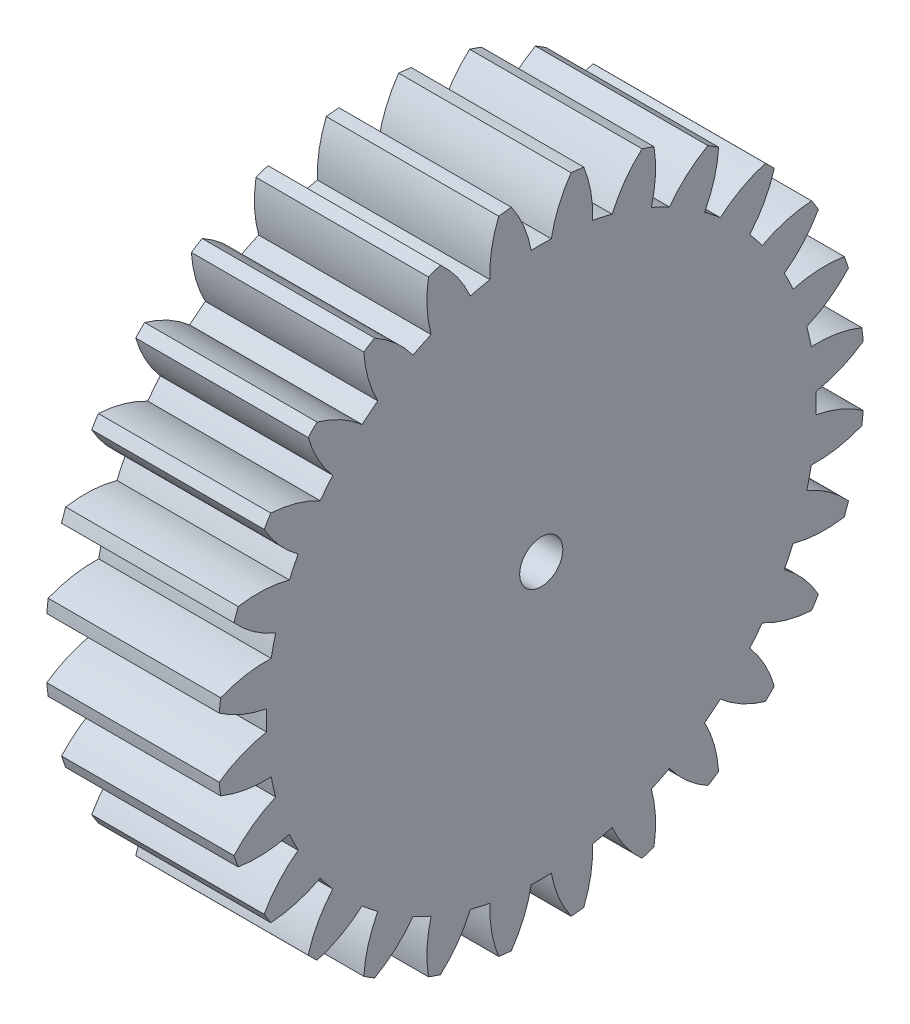
SolidWorks part; units mm, degrees
ref_plane "Plane1" through (0, 0, 0) normal (0, 0, 1) x (1, 0, 0)
ref_plane "Plane2" through (0, 0, 0) normal (0, 1, 0) x (1, 0, 0)
ref_plane "Plane3" through (0, 0, 0) normal (1, 0, 0) x (0, 0, -1)
sketch "HoldingSke" plane through (0, 0, 0) normal (0, 1, 0) x (1, 0, 0)
  line L0 (0, 0) -> (0.3532, -0.1878)
  line L1 (-15, 0) -> (100, 0) construction
  line L2 (0, 0) -> (-2.1039, 2.3779)
  line L3 (0, 0) -> (-11.863, 4.5341)
  line L4 (0, 0) -> (7.6251, 4.0544)
  line L5 (0, 0) -> (-46.8476, -17.4728)
  line L6 (0, 0) -> (-16.5793, -11.1861)
  line L7 (-2.1039, 2.3779) -> (8.6586, 51.2059)
  line L8 (-76.2, 54.61) -> (-75.3, 54.61)
  line L9 (-71.009, 38.7566) -> (-53.1078, 45.2721)
  line L10 (-76.2, 71.12) -> (104.1128, 71.12)
  line L11 (0, 0) -> (-20, 0)
  line L12 (-76.2, 101.6) -> (-76.113, 101.6)
  line L13 (24.9733, 27.94) -> (52.9518, 28.4284)
  line L14 (24.9733, 27.94) -> (24.9743, 27.94)
  line L15 (24.9733, 27.94) -> (100.4006, 29.5858)
  line L16 (-63.627, -2.5) -> (-12.827, -2.5)
  circle A0 centre (0, 0) radius 2.5
  circle A1 centre (0, 0) radius 31.874
  circle A2 centre (0, 0) radius 37.5
  circle A3 centre (0, 0) radius 2.5
  dimension "MHD" = 63.748
  dimension "Hub_dia" = 75
  dimension "Bore" = 5
  dimension "MBD" = 5
  dimension "Num_teeth" = 28
  dimension "Pitch" = 0.4
  dimension "Overall_len" = 50
  dimension "Show_teeth" = 28
  dimension "Thickness" = 20
  dimension "OAL" = 50.0001
  dimension "T_dim" = 0.9
  dimension "Ap" = 20
  dimension "H" = 19.05
  dimension "Pitch_radius" = 180.3128
  dimension "Width" = 20
  dimension "Backlash" = 0.087
  dimension "Addendum_fac" = 1
  dimension "Dedendum_fac" = 1.25
  dimension "Clearance_fac" = 0.25
  dimension "Dedendum_add" = 0.001
  dimension "Module" = 2.5
sketch "BasProSke" plane through (0, 0, 0) normal (0, 1, 0) x (1, 0, 0)
  line L0 (-10, 0) -> (60, 0) construction
  line L1 (0, 0) -> (0, 37.5)
  line L2 (0, 0) -> (20, 0)
  line L3 (20, 0) -> (20, 37.5)
  line L4 (20, 37.5) -> (0, 37.5)
  dimension "Thickness" = 20
  dimension "Diameter" = 75
revolve "Base-Revolve" add sketch "BasProSke" angle 360 about L0
sketch "TooCutSke" plane through (0, 0, 0) normal (1, 0, 0) x (0, 0, -1)
  line L1 (0, 0) -> (0, 107) construction
  line L2 (0, 0) -> (-2.1147, 34.9361) construction
  line L3 (0, 0) -> (-7.827, 69.4668) construction
  line L4 (-2.1147, 34.9361) -> (-3.9135, 34.7334) construction
  arc A0 (1.1659, 31.8527) -> (-1.1659, 31.8527) centre (0, 0) ccw
  arc A1 (3.4842, 37.3633) -> (-3.4842, 37.3633) centre (0, 0) ccw
  circle A2 centre (0, 0) radius 35 construction
  circle A3 centre (0, 0) radius 32.8892 construction
  arc A4 (-1.1659, 31.8527) -> (-3.4842, 37.3633) centre (-14.932, 29.3042) ccw
  arc A5 (3.4842, 37.3633) -> (1.1659, 31.8527) centre (14.932, 29.3042) ccw
  dimension "Root_dia" = 63.748
  dimension "Overcut_dia" = 75.0508
  dimension "Pitch_dia" = 70
  dimension "Base_dia" = 65.7785
  dimension "Flank_rad" = 14
  dimension "Half_ang" = 6.429
  dimension "Half_CT" = 1.8102
extrude "ToothCut" cut sketch "TooCutSke" along normal through all
fillet "Breaks" [suppressed] radius 0.05
fillet "RootFillets" [suppressed] radius 0.626
pattern_circular "TeethCuts" count 28 every 12.857 about axis through (-10, 0, 0) along (1, 0, 0) of "ToothCut", "RootFillets", "Breaks"
sketch "HubNeaOneSke" plane through (0, 0, 0) normal (-1, 0, 0) x (0, 0, 1)
  circle A0 centre (0, 0) radius 31.874
  dimension "Diameter" = 63.748
extrude "HubNearOne" [suppressed] add sketch "HubNeaOneSke" along normal blind 30.0001
sketch "HubNeaBotSke" plane through (0, 0, 0) normal (-1, 0, 0) x (0, 0, 1)
  circle A0 centre (0, 0) radius 31.874
  dimension "Diameter" = 63.748
extrude "HubNearBoth" [suppressed] add sketch "HubNeaBotSke" along normal blind 15
ref_plane "FarPln" through (20, 0, 0) normal (1, 0, 0) x (0, 0, -1)
sketch "HubFarSke" plane through (20, 0, 0) normal (1, 0, 0) x (0, 0, -1)
  circle A0 centre (0, 0) radius 31.874
  dimension "Diameter" = 63.748
extrude "HubFar" [suppressed] add sketch "HubFarSke" along normal blind 15
sketch "BorSke" plane through (0, 0, 0) normal (1, 0, 0) x (0, 0, -1)
  circle A0 centre (0, 0) radius 2.5
  dimension "Diameter" = 5
extrude "Bore" cut sketch "BorSke" along normal mid plane 100.0001
sketch "KeySke" plane through (0, 0, 0) normal (1, 0, 0) x (0, 0, -1)
  line L0 (-1, 0) -> (-1, 3.4)
  line L1 (-1, 3.4) -> (1, 3.4)
  line L2 (1, 3.4) -> (1, 0)
  line L3 (0, 0) -> (0, 34) construction
  line L4 (-1, 0) -> (1, 0)
  dimension "Offset" = 3.4
extrude "Keyway" [suppressed] cut sketch "KeySke" along normal mid plane 100.0001
pattern_circular "Keyway2" [suppressed] count 2 every 90 about axis through (-10, 0, 0) along (1, 0, 0)
equation "' \"Module@HoldingSke\" = 6.35"
equation "' \"Num_teeth@HoldingSke\" = 12"
equation "' \"Ap@HoldingSke\" =  20"
equation "' \"Ap@HoldingSke\" = 20"
equation "' \"Width@HoldingSke\" = 0.5 * 25.4"
equation "' \"Hub_dia@HoldingSke\"= 1 * 25.4"
equation "' \"Hub_dia@HoldingSke\" = 1 * 25.4"
equation "' \"Overall_len@HoldingSke\" = 1.0 * 25.4"
equation "' \"Bore@HoldingSke\" = 0.75 * 25.4"
equation "' \"T_dim@HoldingSke\" = 0.1 * 25.4"
equation "' \"Width@KeySke\" = 0.25 * 25.4"
equation "' \"Show_teeth@HoldingSke\" = 13"
equation "' \"Backlash@HoldingSke\" = 0.009 * 25.4"
equation "' \"Addendum_fac@HoldingSke\" = 1.0"
equation "' \"Dedendum_fac@HoldingSke\" = 1.25"
equation "' \"Dedendum_add@HoldingSke\" = 0.00005 * 25.4"
equation "' \"Clearance_fac@HoldingSke\" = 0.25"
equation "\"Pitch@HoldingSke\" = 1 / \"Module@HoldingSke\""
equation "\"Overcut_dia@TooCutSke\" = (\"Num_teeth@HoldingSke\" + 2 * \"Addendum_fac@HoldingSke\") / \"Pitch@HoldingSke\" + 0.002 * 25.4"
equation "\"Pitch_dia@TooCutSke\" = \"Num_teeth@HoldingSke\" / \"Pitch@HoldingSke\""
equation "\"Base_dia@TooCutSke\" = \"Num_teeth@HoldingSke\" / \"Pitch@HoldingSke\" * cos((\"Ap@HoldingSke\"  * 3.14159265 / 180))"
equation "\"Root_dia@TooCutSke\" = (\"Num_teeth@HoldingSke\" + 2) / \"Pitch@HoldingSke\" - 2 * (\"Addendum_fac@HoldingSke\" + \"Dedendum_fac@HoldingSke\") / \"Pitch@HoldingSke\" - \"Dedendum_add@HoldingSke\" * 2"
equation "\"Half_ang@TooCutSke\" = 180 / \"Num_teeth@HoldingSke\""
equation "\"Half_CT@TooCutSke\" = \"Num_teeth@HoldingSke\" / \"Pitch@HoldingSke\" * sin((3.14159265 / 2 / \"Num_teeth@HoldingSke\")) / 2 - 7 * \"Backlash@HoldingSke\" / 4"
equation "\"Flank_rad@TooCutSke\" = \"Num_teeth@HoldingSke\" / \"Pitch@HoldingSke\" / 5"
equation "\"Radius@RootFillets\" = \"Clearance_fac@HoldingSke\" / \"Pitch@HoldingSke\" + \"Dedendum_add@HoldingSke\""
equation "\"Break_rad@Breaks\" = 0.02 / \"Pitch@HoldingSke\""
equation "\"Thickness@HoldingSke\" = \"Width@HoldingSke\""
equation "\"OAL@HoldingSke\" = \"Thickness@HoldingSke\""
equation "\"MHD@HoldingSke\" = (\"Num_teeth@HoldingSke\" + 2) / \"Pitch@HoldingSke\" - 2 * (\"Addendum_fac@HoldingSke\" + \"Dedendum_fac@HoldingSke\")  / \"Pitch@HoldingSke\" - \"Dedendum_add@HoldingSke\" * 2"
equation "\"MBD@HoldingSke\" = (\"Num_teeth@HoldingSke\" + 2) / \"Pitch@HoldingSke\" - 2 * (\"Addendum_fac@HoldingSke\" + \"Dedendum_fac@HoldingSke\")  / \"Pitch@HoldingSke\" - \"Dedendum_add@HoldingSke\" * 2 - 0.002 * 25.4"
equation "\"MHD@HoldingSke\" = ((sgn( \"MHD@HoldingSke\" - \"Hub_dia@HoldingSke\" )-1)*( \"MHD@HoldingSke\" - \"Hub_dia@HoldingSke\" ))/-2+ \"Hub_dia@HoldingSke\""
equation "\"MBD@HoldingSke\" = ((sgn( \"MBD@HoldingSke\" - \"Bore@HoldingSke\" )-1)*( \"MBD@HoldingSke\" - \"Bore@HoldingSke\" ))/-2+ \"Bore@HoldingSke\""
equation "\"OAL@HoldingSke\" = ((sgn( \"OAL@HoldingSke\" - \"Overall_len@HoldingSke\" )+1)*( \"OAL@HoldingSke\" - \"Overall_len@HoldingSke\" ))/2 + \"Overall_len@HoldingSke\" + 0.000002 * 25.4"
equation "\"Num_teeth@TeethCuts\" = int( \"Show_teeth@HoldingSke\" ) + 1"
equation "\"Num_teeth@TeethCuts\" = ((sgn( \"Num_teeth@TeethCuts\" - \"Num_teeth@HoldingSke\" )-1)*( \"Num_teeth@TeethCuts\" - \"Num_teeth@HoldingSke\" ))/-2+ \"Num_teeth@HoldingSke\""
equation "\"Num_teeth@TeethCuts\" = ((sgn( \"Num_teeth@TeethCuts\" - 2.0)+1)*( \"Num_teeth@TeethCuts\" - 2.0))/2 +2.0"
equation "\"Angle@TeethCuts\" = 360.0 / \"Num_teeth@HoldingSke\""
equation "\"Diameter@BasProSke\" = (\"Num_teeth@HoldingSke\" + 2 * \"Addendum_fac@HoldingSke\") / \"Pitch@HoldingSke\""
equation "\"Thickness@BasProSke\"  = \"Thickness@HoldingSke\""
equation "' \"Fillet_rad@BasProSke\" =  \"Thickness@HoldingSke\" * 0.05"
equation "' \"Fillet_rad@BasProSke\" = \"Thickness@HoldingSke\" * 0.05"
equation "\"MHD@HoldingSke\" = ((sgn( \"MHD@HoldingSke\" - \"Root_dia@TooCutSke\" )-1)*( \"MHD@HoldingSke\" - \"Root_dia@TooCutSke\" ))/-2+ \"Root_dia@TooCutSke\""
equation "\"Diameter@HubNeaOneSke\" = \"MHD@HoldingSke\""
equation "\"Length@HubNearOne\" = \"OAL@HoldingSke\" - \"Thickness@BasProSke\""
equation "\"Diameter@HubNeaBotSke\" = \"MHD@HoldingSke\""
equation "\"Length@HubNearBoth\" = ( \"OAL@HoldingSke\" - \"Thickness@BasProSke\" ) / 2.0"
equation "\"Thickness@FarPln\" = \"Thickness@BasProSke\""
equation "\"Diameter@HubFarSke\" = \"MHD@HoldingSke\""
equation "\"Length@HubFar\" = ( \"OAL@HoldingSke\" - \"Thickness@BasProSke\" ) / 2.0"
equation "\"Diameter@BorSke\" = \"MBD@HoldingSke\""
equation "\"D1@Bore\" = \"OAL@HoldingSke\" * 2.0"
equation "\"D1@Keyway\" = \"OAL@HoldingSke\" * 2.0"
equation "\"Offset@KeySke\" = \"T_dim@HoldingSke\" + \"MBD@HoldingSke\" / 2.0"
